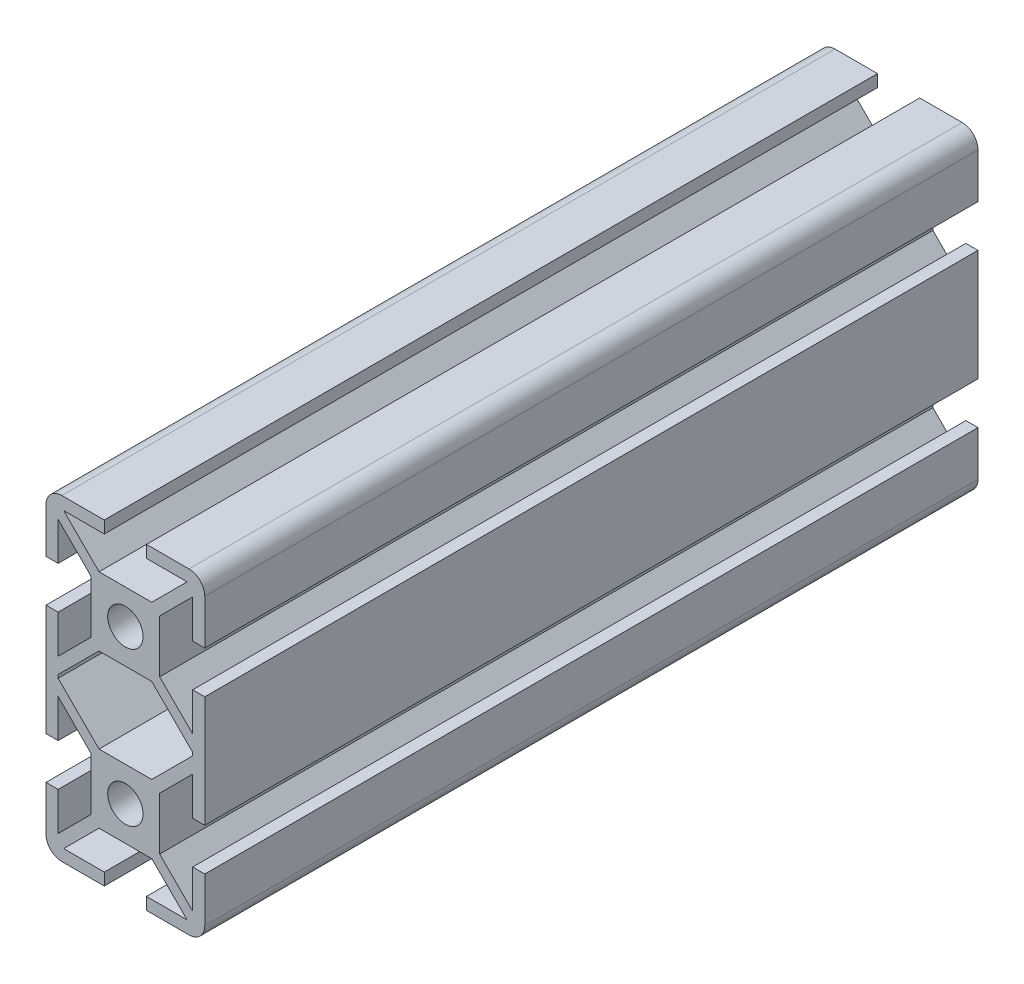
SolidWorks part; units mm, degrees
ref_plane "Alzado" through (0, 0, 0) normal (0, 0, 1) x (1, 0, 0)
ref_plane "Planta" through (0, 0, 0) normal (0, 1, 0) x (1, 0, 0)
ref_plane "Vista lateral" through (0, 0, 0) normal (1, 0, 0) x (0, 0, -1)
sketch "Croquis1" plane through (0, 0, 0) normal (0, 0, 1) x (1, 0, 0)
  line L0 (-15.05, 0) -> (15.05, 0) construction
  line L1 (-12.05, -30.05) -> (-4, -30.05)
  line L2 (-15.05, -27.05) -> (-15.05, -18.55)
  line L3 (-12.05, 30.05) -> (-4, 30.05)
  line L4 (15.05, -27.05) -> (15.05, -18.55)
  line L5 (-15.05, -30.05) -> (15.05, 30.05) construction
  line L6 (-15.05, 30.05) -> (15.05, -30.05) construction
  line L7 (-4, 30.05) -> (-4, 27.75)
  line L8 (-5, 8.05) -> (5, 8.05)
  line L9 (-6.5, 9.55) -> (-6.5, 19.55)
  line L10 (-5, 21.05) -> (5, 21.05)
  line L11 (6.5, 9.55) -> (6.5, 19.55)
  line L12 (-6.5, 8.05) -> (6.5, 21.05) construction
  line L13 (-6.5, 21.05) -> (6.5, 8.05) construction
  line L14 (15.05, 18.55) -> (15.05, 27.05)
  line L15 (-3.35, 11.2) -> (3.35, 11.2) construction
  line L16 (-3.35, 11.2) -> (-3.35, 17.9) construction
  line L17 (-3.35, 17.9) -> (3.35, 17.9) construction
  line L18 (3.35, 11.2) -> (3.35, 17.9) construction
  line L19 (-3.35, 11.2) -> (3.35, 17.9) construction
  line L20 (-3.35, 17.9) -> (3.35, 11.2) construction
  line L21 (-11.7, -27.75) -> (-4, -27.75)
  line L22 (-12.75, -25.8) -> (-12.75, -18.55)
  line L23 (-11.7, 27.75) -> (-4, 27.75)
  line L24 (12.75, -25.8) -> (12.75, -18.55)
  line L25 (-12.75, -27.75) -> (12.75, 27.75) construction
  line L26 (-12.75, 27.75) -> (12.75, -27.75) construction
  line L27 (4, 30.05) -> (4, 27.75)
  line L28 (12.75, 18.55) -> (12.75, 25.8)
  line L31 (-15.05, 18.55) -> (-12.75, 18.55)
  line L32 (-15.05, 10.55) -> (-12.75, 10.55)
  line L33 (15.05, 10.55) -> (12.75, 10.55)
  line L34 (15.05, 18.55) -> (12.75, 18.55)
  line L36 (-5, 21.05) -> (-11.7, 27.75)
  line L37 (-6.5, 21.05) -> (-12.75, 27.75) construction
  line L39 (-6.5, 19.55) -> (-12.75, 25.8)
  line L40 (6.5, 19.55) -> (12.75, 25.8)
  line L41 (5, 21.05) -> (11.7, 27.75)
  line L42 (6.5, -19.55) -> (12.75, -25.8)
  line L43 (5, -21.05) -> (11.7, -27.75)
  line L44 (-15.05, -30.05) -> (-4, -30.05)
  line L45 (-15.05, 30.05) -> (-4, 30.05)
  line L46 (-6.5, -19.55) -> (-12.75, -25.8)
  line L47 (-5, -21.05) -> (-11.7, -27.75)
  line L48 (4, -30.05) -> (4, -27.75)
  line L49 (-4, -30.05) -> (-4, -27.75)
  line L50 (-15.05, -10.55) -> (-12.75, -10.55)
  line L51 (-15.05, -18.55) -> (-12.75, -18.55)
  line L52 (15.05, -18.55) -> (12.75, -18.55)
  line L53 (15.05, -10.55) -> (12.75, -10.55)
  line L54 (-3.35, -11.2) -> (-3.35, -17.9) construction
  line L55 (-3.35, -17.9) -> (3.35, -17.9) construction
  line L56 (3.35, -11.2) -> (3.35, -17.9) construction
  line L57 (-3.35, -11.2) -> (3.35, -11.2) construction
  line L58 (-5, -8.05) -> (5, -8.05)
  line L59 (6.5, -9.55) -> (6.5, -19.55)
  line L60 (-6.5, -9.55) -> (-6.5, -19.55)
  line L61 (-5, -21.05) -> (5, -21.05)
  line L62 (4, -30.05) -> (12.05, -30.05)
  line L63 (6.5, -9.55) -> (12.75, -3.3)
  line L64 (5, -8.05) -> (11.7, -1.35)
  line L65 (-5, -8.05) -> (-11.7, -1.35)
  line L66 (-6.5, -9.55) -> (-12.75, -3.3)
  line L67 (-11.7, -1.35) -> (-12.75, -0.3)
  line L68 (11.7, -1.35) -> (12.75, -0.3)
  line L69 (-12.75, -0.3) -> (-12.75, 0.3)
  line L70 (12.75, -0.3) -> (12.75, 0.3)
  line L71 (6.5, 9.55) -> (12.75, 3.3)
  line L72 (5, 8.05) -> (11.7, 1.35)
  line L73 (-6.5, 9.55) -> (-12.75, 3.3)
  line L74 (-5, 8.05) -> (-11.7, 1.35)
  line L75 (-11.7, 1.35) -> (-12.75, 0.3)
  line L76 (11.7, 1.35) -> (12.75, 0.3)
  line L77 (-12.75, 3.3) -> (-12.75, 10.55)
  line L78 (12.75, 3.3) -> (12.75, 10.55)
  line L79 (15.05, -10.55) -> (15.05, 10.55)
  line L80 (12.75, -10.55) -> (12.75, -3.3)
  line L81 (-15.05, -10.55) -> (-15.05, 10.55)
  line L82 (-12.75, -10.55) -> (-12.75, -3.3)
  line L83 (4, -30.05) -> (15.05, -30.05)
  line L84 (4, -27.75) -> (11.7, -27.75)
  line L85 (4, 30.05) -> (12.05, 30.05)
  line L86 (4, 30.05) -> (15.05, 30.05)
  line L87 (4, 27.75) -> (11.7, 27.75)
  line L88 (-12.75, 18.55) -> (-12.75, 25.8)
  line L89 (-15.05, 18.55) -> (-15.05, 27.05)
  arc A0 (-12.05, -30.05) -> (-15.05, -27.05) centre (-12.05, -27.05) cw
  arc A1 (12.05, -30.05) -> (15.05, -27.05) centre (12.05, -27.05) ccw
  arc A2 (12.05, 30.05) -> (15.05, 27.05) centre (12.05, 27.05) cw
  arc A3 (-15.05, 27.05) -> (-12.05, 30.05) centre (-12.05, 27.05) cw
  circle A4 centre (0, 14.55) radius 3.35
  circle A5 centre (0, -14.55) radius 3.35
  point P0 (0, 0)
  point P8 (0, 14.55)
  point P9 (0, 14.55)
  point P20 (0, 0)
  point P55 (0, 11.2)
  point P72 (0, -11.2)
  dimension "D10" = 3
  dimension "D1" = 60.1
  dimension "D2" = 30.1
  dimension "D3" = 13
  dimension "D4" = 13
  dimension "D5" = 22
  dimension "D6" = 25.5
  dimension "D7" = 6.7
  dimension "D8" = 6.7
  dimension "D9" = 55.5
  dimension "D12" = 1.5
  dimension "D13" = 135
  dimension "D14" = 1.5
  dimension "D15" = 135
extrude "Saliente-Extruir1" add sketch "Croquis1" along normal blind 146.6 contours A3 L89 L31 L88 L39 L9 L73 L77 L32 L81 L50 L82 L66 L60 L46 L22 L51 L2 A0 L1 L49 L21 L47 L61 L43 L84 L48 L62 A1 L4 L52 L24 L42 L59 L63 L80 L53 L79 L33 L78 L71 L11 L40 L28 L34 L14 A2 L85 L27 L87 L41
